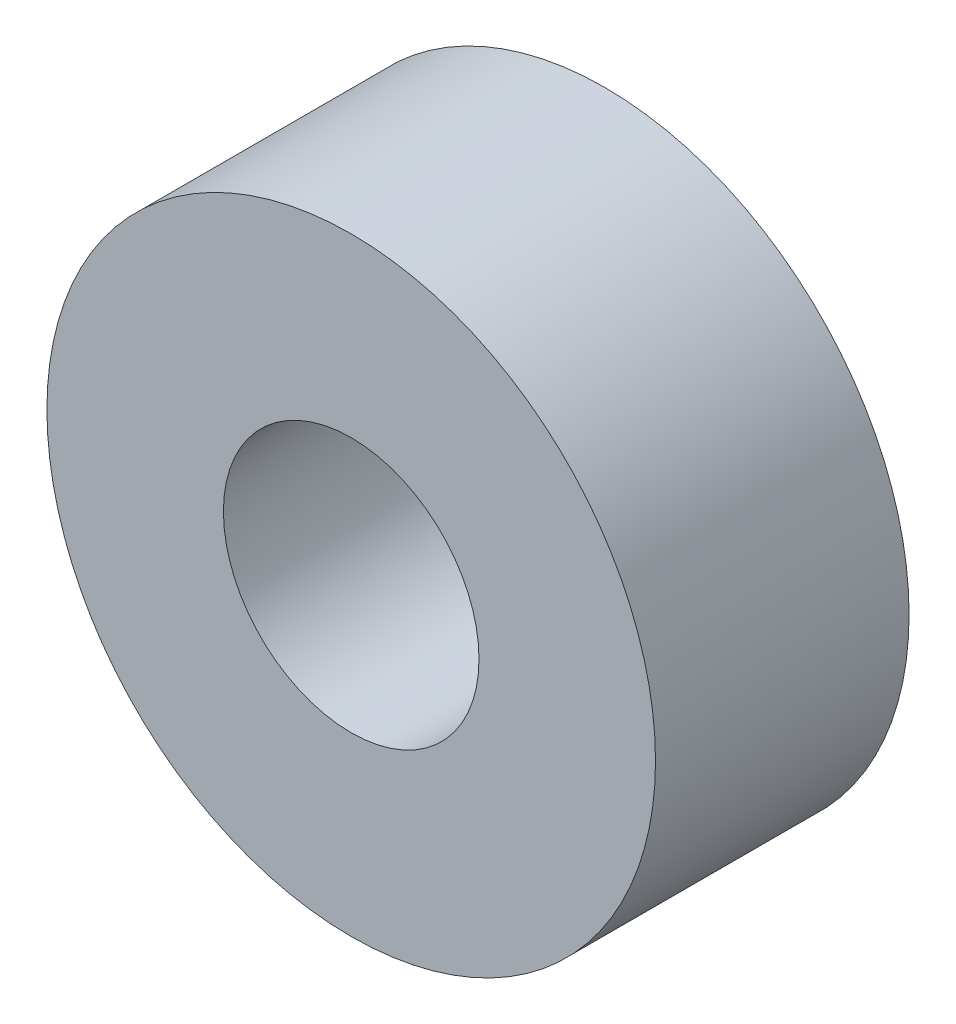
SolidWorks part; units mm, degrees
ref_plane "Front Plane" through (0, 0, 0) normal (0, 0, 1) x (1, 0, 0)
ref_plane "Top Plane" through (0, 0, 0) normal (0, 1, 0) x (1, 0, 0)
ref_plane "Right Plane" through (0, 0, 0) normal (1, 0, 0) x (0, 0, -1)
sketch "Sketch1" plane through (0, 0, 0) normal (0, 0, 1) x (1, 0, 0)
  circle A0 centre (0, 0) radius 9.525
  circle A1 centre (0, 0) radius 4.0005
  dimension "OD" = 19.05
  dimension "ID" = 8.001
extrude "Extrude1" add sketch "Sketch1" along normal mid plane 7.9375
sketch "Sketch2" plane through (0, 0, 0) normal (1, 0, 0) x (0, 0, -1)
  line L0 (-3.9688, -4.0005) -> (3.9688, -4.0005) construction
  line L3 (3.9688, 4.0005) -> (-3.9688, 4.0005) construction
  line L5 (-3.9688, -4.0005) -> (3.9688, -4.0005)
  line L6 (3.9688, 4.0005) -> (-3.9688, 4.0005)
sketch "Sketch4" plane through (0, 0, 3.9688) normal (0, 0, 1) x (1, 0, 0)
  line L0 (0, 0) -> (-2.8288, 2.8288)
  line L1 (0, -2.1828) -> (0, 2.1828) construction
  circle A0 centre (0, 0) radius 4.0005 construction
  dimension "D1" = 45
